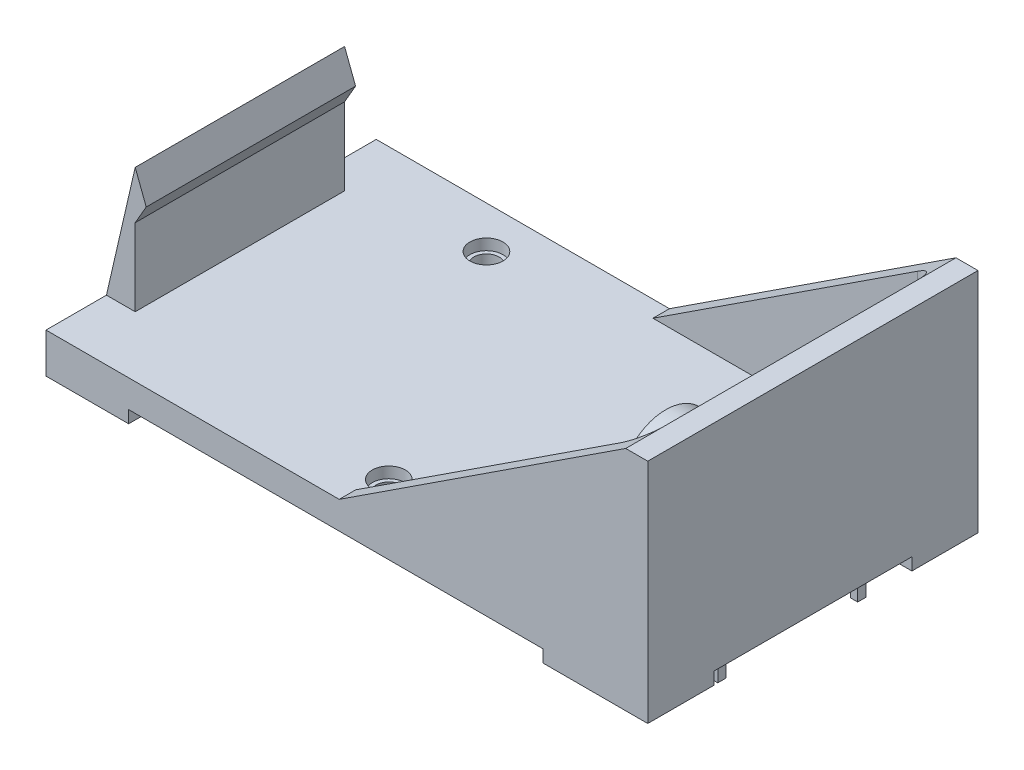
SolidWorks part; units mm, degrees
material "PUR"
ref_plane "Спереди" through (0, 0, 0) normal (0, 0, 1) x (1, 0, 0)
ref_plane "Сверху" through (0, 0, 0) normal (0, 1, 0) x (1, 0, 0)
ref_plane "Справа" through (0, 0, 0) normal (1, 0, 0) x (0, 0, -1)
sketch "Эскиз1" plane through (0, 0, 0) normal (0, 1, 0) x (1, 0, 0)
  line L1 (-27.305, 14.985) -> (27.305, 14.985)
  line L2 (-27.305, 14.985) -> (-27.305, -14.985)
  line L3 (-27.305, -14.985) -> (27.305, -14.985)
  line L4 (27.305, 14.985) -> (27.305, -14.985)
  line L5 (-27.305, 14.985) -> (27.305, -14.985) construction
  line L6 (-27.305, -14.985) -> (27.305, 14.985) construction
  point P0 (0, 0)
  dimension "D1" = 29.97
  dimension "D2" = 54.61
extrude "Бобышка-Вытянуть1" add sketch "Эскиз1" along normal blind 2.5
sketch "Эскиз2" plane through (0, 2.5, 0) normal (0, 1, 0) x (1, 0, 0)
  line L0 (27.305, -14.985) -> (-0.695, -14.985)
  line L1 (-27.305, -14.985) -> (27.305, -14.985) construction
  line L2 (-0.695, -14.985) -> (-0.695, -13.485)
  line L3 (-0.695, -13.485) -> (23.305, -13.485)
  line L4 (25.305, -11.485) -> (25.305, 11.485)
  line L5 (27.305, -14.985) -> (27.305, 14.985)
  line L6 (27.305, -14.985) -> (27.305, 14.985) construction
  line L7 (34.4496, 0) -> (-14.6404, 0) construction
  line L8 (27.305, 14.985) -> (-0.695, 14.985)
  line L9 (-0.695, 14.985) -> (-0.695, 13.485)
  line L10 (-0.695, 13.485) -> (23.305, 13.485)
  arc A0 (25.305, -11.485) -> (23.305, -13.485) centre (23.305, -11.485) cw
  arc A1 (25.305, 11.485) -> (23.305, 13.485) centre (23.305, 11.485) ccw
  point P17 (27.305, 0)
  point P22 (25.305, 0)
  dimension "D4" = 2
  dimension "D1" = 1.5
  dimension "D2" = 2
  dimension "D3" = 28
extrude "Бобышка-Вытянуть2" add sketch "Эскиз2" along normal blind 17
sketch "Эскиз3" plane through (0, 0, 14.985) normal (0, 0, 1) x (1, 0, 0)
  line L0 (-0.695, 2.5) -> (25.305, 19.5)
  line L1 (-0.695, 19.5) -> (27.305, 19.5) construction
  line L2 (25.305, 19.5) -> (-0.695, 19.5)
  line L3 (-0.695, 19.5) -> (-0.695, 2.5)
extrude "Вырез-Вытянуть1" cut sketch "Эскиз3" against normal through all
sketch "Эскиз4" plane through (0, 2.5, 0) normal (0, 1, 0) x (1, 0, 0)
  line L0 (0, 0) -> (36.3439, 0) construction
  line L1 (-34.9908, 11.175) -> (34.2331, 11.175) construction
  line L2 (-15.0193, -11.175) -> (34.2331, -11.175) construction
  line L3 (27.305, -14.985) -> (27.305, 14.985) construction
  circle A0 centre (-13.495, 11.175) radius 1.145
  circle A1 centre (-0.005, -11.175) radius 1.145
  circle A2 centre (13.475, 11.175) radius 1.145
  dimension "D1" = 2.29
  dimension "D2" = 22.35
  dimension "D3" = 27.31
  dimension "D4" = 13.49
  dimension "D5" = 26.97
extrude "Вырез-Вытянуть2" cut sketch "Эскиз4" against normal through all
sketch "Эскиз5" plane through (0, 0, 0) normal (0, -1, 0) x (1, 0, 0)
  line L1 (-27.305, 14.985) -> (-19.805, 14.985)
  line L2 (-27.305, 14.985) -> (-27.305, 8.985)
  line L3 (-27.305, 8.985) -> (-19.805, 8.985)
  line L4 (-19.805, 14.985) -> (-19.805, 8.985)
  line L5 (27.305, 14.985) -> (17.805, 14.985)
  line L6 (27.305, 14.985) -> (27.305, 8.985)
  line L7 (27.305, 8.985) -> (17.805, 8.985)
  line L8 (17.805, 14.985) -> (17.805, 8.985)
  line L9 (27.305, -14.985) -> (17.805, -14.985)
  line L10 (27.305, -14.985) -> (27.305, -8.985)
  line L11 (27.305, -8.985) -> (17.805, -8.985)
  line L12 (17.805, -14.985) -> (17.805, -8.985)
  line L13 (-27.305, -14.985) -> (-19.805, -14.985)
  line L14 (-27.305, -14.985) -> (-27.305, -8.985)
  line L15 (-27.305, -8.985) -> (-19.805, -8.985)
  line L16 (-19.805, -14.985) -> (-19.805, -8.985)
  circle A0 centre (-0.005, 11.175) radius 2.25
  circle A1 centre (13.475, -11.175) radius 2.25
  circle A2 centre (-13.495, -11.175) radius 2.25
  dimension "D1" = 4.5
  dimension "D2" = 6
  dimension "D3" = 9.5
  dimension "D4" = 7.5
extrude "Бобышка-Вытянуть3" add sketch "Эскиз5" along direction (0, -1, 0) on the side of the normal offset from surface (1.12 mm away) 20.62
sketch "Эскиз6" plane through (0, 2.5, 0) normal (0, 1, 0) x (1, 0, 0)
  circle A15 centre (-13.495, 11.175) radius 1.145
  circle A16 centre (-13.495, 11.175) radius 1.145
  circle A18 centre (13.475, 11.175) radius 1.145
  circle A19 centre (13.475, 11.175) radius 1.145
  circle A21 centre (-0.005, -11.175) radius 1.145
  circle A22 centre (-0.005, -11.175) radius 1.145
  dimension "D1" = 0
  dimension "D2" = 0
  dimension "D3" = 0
extrude "Вырез-Вытянуть3" cut sketch "Эскиз6" against normal through all
sketch "Эскиз7" plane through (0, 2.5, 0) normal (0, 1, 0) x (1, 0, 0)
  circle A0 centre (-13.495, 11.175) radius 1.5
  circle A1 centre (13.475, 11.175) radius 1.5
  circle A2 centre (-0.005, -11.175) radius 1.5
  dimension "D1" = 3
extrude "Вырез-Вытянуть4" cut sketch "Эскиз7" against normal blind 1
sketch "Эскиз8" plane through (0, 0, 0) normal (0, 0, 1) x (1, 0, 0)
  line L0 (-27.305, 2.5) -> (-24.695, 13.85)
  line L1 (-24.695, 13.85) -> (-23.695, 11.2321)
  line L2 (-23.695, 11.2321) -> (-24.695, 9.5)
  line L3 (-24.695, 9.5) -> (-24.695, 2.5)
  line L4 (-27.305, 2.5) -> (-0.695, 2.5) construction
  line L5 (-24.695, 2.5) -> (-27.305, 2.5)
  line L6 (-27.305, -1.12) -> (-19.805, -1.12) construction
  dimension "D1" = 14.97
  dimension "D2" = 49
  dimension "D3" = 7
  dimension "D4" = 1
  dimension "D5" = 2
extrude "Бобышка-Вытянуть4" add sketch "Эскиз8" along normal blind 9.5 and the other way blind 9.5
sketch "Эскиз9" plane through (0, 0, 0) normal (0, -1, 0) x (1, 0, 0)
  line L0 (25.075, 20.363) -> (25.075, -22.124) construction
  line L1 (36.5427, 0) -> (8.3422, 0) construction
  line L2 (24.745, 5.97) -> (25.405, 5.97)
  line L3 (24.745, -6.73) -> (25.405, -6.73)
  line L4 (24.745, -6.73) -> (24.745, -5.97)
  line L5 (24.745, -5.97) -> (25.405, -5.97)
  line L6 (25.405, -6.73) -> (25.405, -5.97)
  line L7 (24.745, -6.73) -> (25.405, -5.97) construction
  line L8 (24.745, -5.97) -> (25.405, -6.73) construction
  line L9 (25.405, 6.73) -> (25.405, 5.97)
  line L10 (24.745, 6.73) -> (25.405, 6.73)
  line L11 (24.745, 6.73) -> (24.745, 5.97)
  circle A0 centre (13.475, -11.175) radius 1.145 construction
  point P4 (25.075, -6.35)
  dimension "D4" = 11.6
  dimension "D1" = 0.76
  dimension "D2" = 0.66
  dimension "D3" = 12.7
extrude "Бобышка-Вытянуть5" add sketch "Эскиз9" along normal blind 3
sketch "Эскиз10" plane through (25.305, 0, 0) normal (-1, 0, 0) x (0, 0, 1)
  line L0 (-18.4903, 11.48) -> (20.51, 11.48) construction
  line L1 (0, 0) -> (0, 20.3244) construction
  line L2 (-14.985, -1.12) -> (-8.985, -1.12) construction
  circle A0 centre (-6.35, 11.48) radius 3.75
  circle A1 centre (6.35, 11.48) radius 3.75
  dimension "D3" = 7.5
  dimension "D1" = 12.6
  dimension "D2" = 12.7
extrude "Бобышка-Вытянуть6" add sketch "Эскиз10" along normal blind 1
sketch "Эскиз11" plane through (24.305, 0, 0) normal (-1, 0, 0) x (0, 0, 1)
  circle A0 centre (-6.35, 11.48) radius 3
  circle A1 centre (-6.35, 11.48) radius 2
  dimension "D1" = 6
  dimension "D2" = 4
extrude "Бобышка-Вытянуть7" add sketch "Эскиз11" along normal blind 4
sketch "Эскиз12" plane through (24.305, 0, 0) normal (-1, 0, 0) x (0, 0, 1)
  circle A0 centre (6.35, 11.48) radius 4.25
  circle A1 centre (6.35, 11.48) radius 3.25
  dimension "D1" = 8.5
  dimension "D2" = 6.5
extrude "Бобышка-Вытянуть8" add sketch "Эскиз12" along normal blind 4
